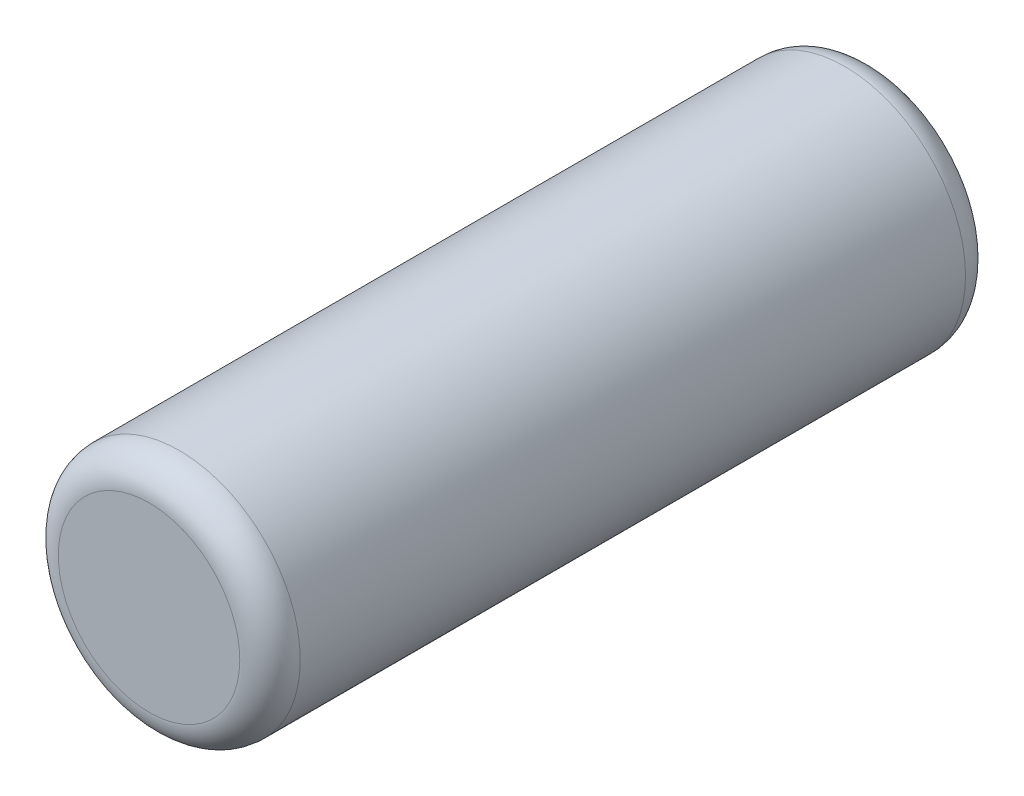
SolidWorks part; units mm, degrees
ref_plane "Front Plane" through (0, 0, 0) normal (0, 0, 1) x (1, 0, 0)
ref_plane "Top Plane" through (0, 0, 0) normal (0, 1, 0) x (1, 0, 0)
ref_plane "Right Plane" through (0, 0, 0) normal (1, 0, 0) x (0, 0, -1)
sketch "Sketch1" plane through (0, 0, 0) normal (0, 0, 1) x (1, 0, 0)
  line L0 (0, 0) -> (-64736.8485, 0) construction
  line L1 (0, 0) -> (0, 64736.8485) construction
  line L4 (-30, 2.5) -> (-30, 42.5)
  line L5 (-30, 42.5) -> (30, 42.5)
  line L12 (-30, 2.5) -> (-85.101, 2.5)
  line L13 (-90, 0) -> (-93.5353, 4.2132) construction
  line L14 (-93.5353, 4.2132) -> (-92.5712, 3.0642)
  line L15 (93.5353, 4.2132) -> (92.5712, 3.0642)
  line L16 (30, 2.5) -> (85.101, 2.5)
  line L17 (30, 2.5) -> (30, 42.5)
  line L18 (30, -2.5) -> (30, -42.5)
  line L19 (30, -2.5) -> (85.101, -2.5)
  line L20 (93.5353, -4.2132) -> (92.5712, -3.0642)
  line L21 (-93.5353, -4.2132) -> (-92.5712, -3.0642)
  line L22 (-30, -2.5) -> (-85.101, -2.5)
  line L23 (-30, -42.5) -> (30, -42.5)
  line L24 (-30, -2.5) -> (-30, -42.5)
  arc A1 (-92.5712, -3.0642) -> (-92.5712, 3.0642) centre (-90, 0) ccw
  arc A8 (-85.101, 2.5) -> (-93.5353, 4.2132) centre (-90, 0) ccw
  arc A9 (85.101, 2.5) -> (93.5353, 4.2132) centre (90, 0) cw
  arc A10 (92.5712, -3.0642) -> (92.5712, 3.0642) centre (90, 0) cw
  arc A11 (85.101, -2.5) -> (93.5353, -4.2132) centre (90, 0) ccw
  arc A12 (-85.101, -2.5) -> (-93.5353, -4.2132) centre (-90, 0) cw
  circle A13 centre (90, 0) radius 4
  point P13 (0, -42.5)
  point P14 (-90, 0)
  point P19 (90, 0)
  point P33 (0, 42.5)
  dimension "D4" = 8
  dimension "D3" = 11
  dimension "D1" = 85
  dimension "D2" = 60
  dimension "D5" = 5
  dimension "D6" = 90
  dimension "D7" = 50
extrude "Boss-Extrude1" add sketch "Sketch1" along normal blind 24 contours A10 A13
fillet "Fillet1" radius 1 2 edges at (94, 0, 24) (94, 0, 0)
